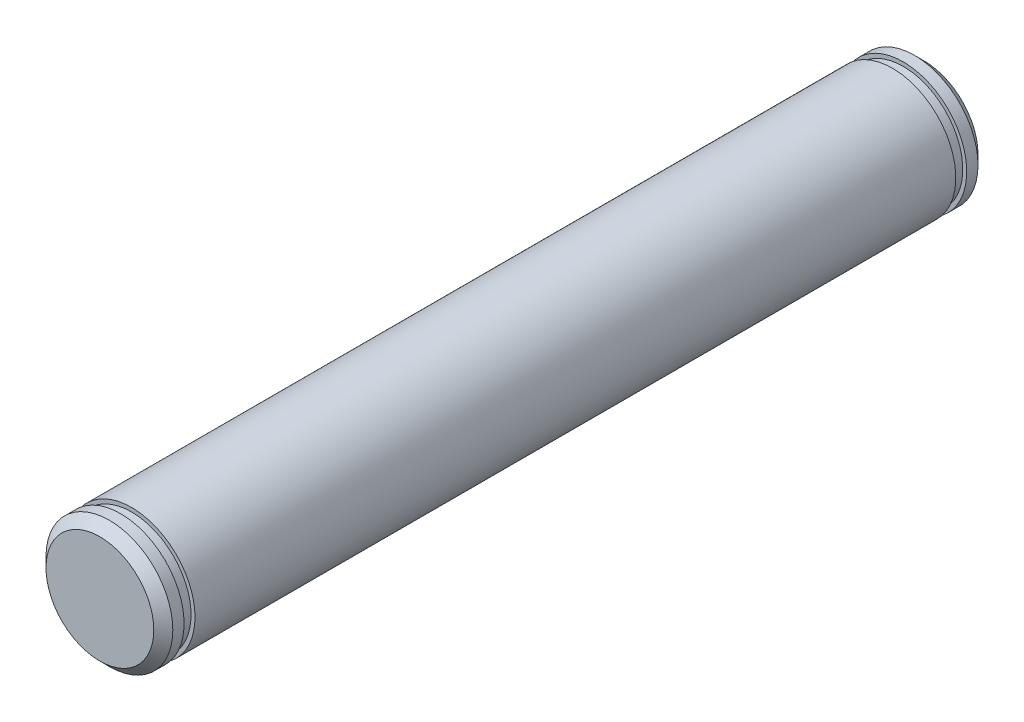
SolidWorks part; units mm, degrees
material "Plain Carbon Steel"
ref_plane "Front Plane" through (0, 0, 0) normal (0, 0, 1) x (1, 0, 0)
ref_plane "Top Plane" through (0, 0, 0) normal (0, 1, 0) x (1, 0, 0)
ref_plane "Right Plane" through (0, 0, 0) normal (1, 0, 0) x (0, 0, -1)
sketch "Sketch1" plane through (0, 0, 0) normal (0, 0, 1) x (1, 0, 0)
  circle A0 centre (0, 0) radius 12.7
  dimension "D1" = 25.4
extrude "Boss-Extrude1" add sketch "Sketch1" along normal blind 165.1
sketch "Sketch2" plane through (0, 0, 0) normal (0, 1, 0) x (1, 0, 0)
  line L0 (0, 0) -> (0, -174.3719) construction
  line L1 (12.7, 0) -> (-12.7, 0) construction
  line L2 (-12.7, 0) -> (-12.7, -165.1) construction
  line L3 (-12.7, -4.1656) -> (-11.9126, -4.1656)
  line L4 (-12.7, -4.1656) -> (-12.7, -6.35)
  line L5 (-12.7, -6.35) -> (-11.9126, -6.35)
  line L6 (-11.9126, -4.1656) -> (-11.9126, -6.35)
  line L8 (-12.7, -158.75) -> (-11.9126, -158.75)
  line L9 (-12.7, -158.75) -> (-12.7, -160.9344)
  line L10 (-12.7, -160.9344) -> (-11.9126, -160.9344)
  line L11 (-11.9126, -158.75) -> (-11.9126, -160.9344)
  dimension "D1" = 6.35
  dimension "D2" = 2.1844
  dimension "D3" = 11.9126
  dimension "D4" = 11.9126
  dimension "D5" = 2.1844
  dimension "D6" = 6.35
revolve "Cut-Revolve1" cut sketch "Sketch2" angle 360 about L0
chamfer "Chamfer1" distance 1.905 angle 45 2 edges at (12.7, 0, 165.1) (12.7, 0, 0)
